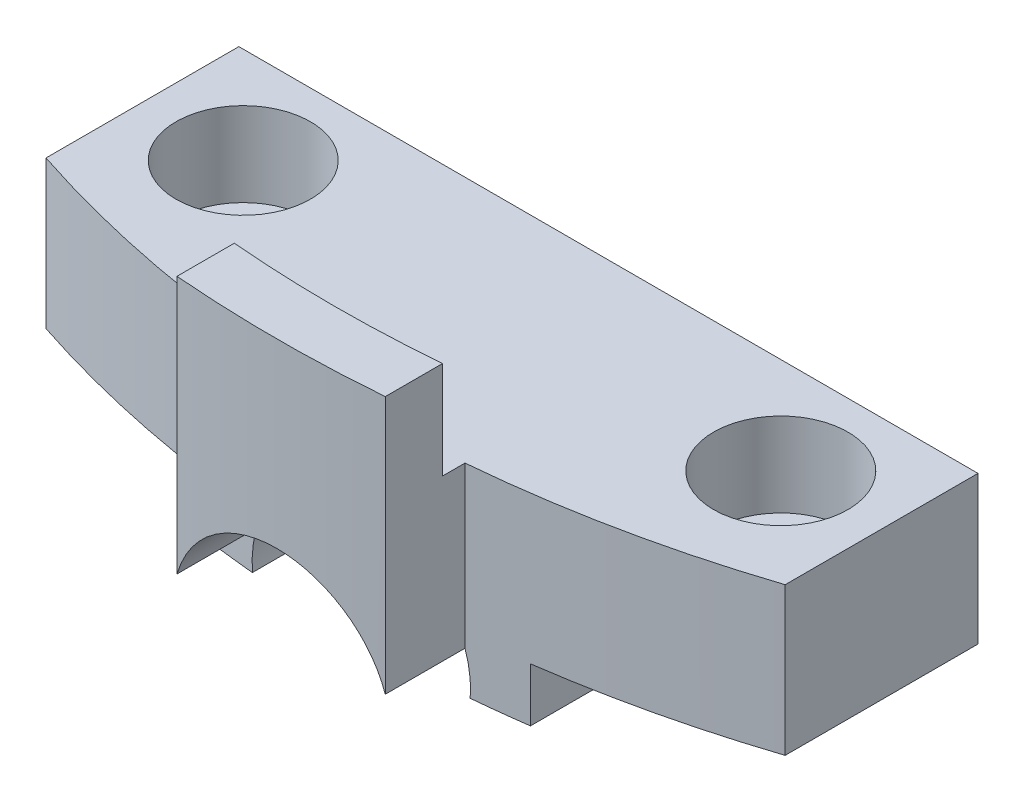
SolidWorks part; units mm, degrees
ref_plane "Front Plane" through (0, 0, 0) normal (0, 0, 1) x (1, 0, 0)
ref_plane "Top Plane" through (0, 0, 0) normal (0, 1, 0) x (1, 0, 0)
ref_plane "Right Plane" through (0, 0, 0) normal (1, 0, 0) x (0, 0, -1)
sketch "Sketch1" plane through (0, 0, 0) normal (0, 1, 0) x (1, 0, 0)
  line L0 (-8, -30.5) -> (8, -30.5) construction
  line L1 (-3.1, -37.3716) -> (-3.1, -34.999)
  line L2 (-11, -27.6303) -> (11, -27.6303)
  line L3 (-11, -27.6303) -> (-11, -33.3697)
  line L5 (11, -27.6303) -> (11, -33.3697)
  line L6 (3.1, -37.3716) -> (3.1, -34.999)
  circle A0 centre (-8, -30.5) radius 1.1
  circle A1 centre (8, -30.5) radius 1.1
  arc A2 (11, -33.3697) -> (3.1, -34.999) centre (0, 0) cw
  arc A3 (-3.1, -37.3716) -> (3.1, -37.3716) centre (0, 0) ccw
  arc A4 (-3.1, -34.999) -> (-11, -33.3697) centre (0, 0) cw
  point P4 (0, -30.5)
  point P10 (0, -27.6303)
  point P12 (-11, -30.5)
  point P15 (0, -37.5)
  dimension "D2" = 2.2
  dimension "D5" = 35.136
  dimension "D6" = 37.5
  dimension "D1" = 16
  dimension "D3" = 22
  dimension "D4" = 30.5
  dimension "D7" = 6.2
extrude "Boss-Extrude1" add sketch "Sketch1" along normal blind 4.4
sketch "Sketch2" plane through (0, 4.4, 0) normal (0, 1, 0) x (1, 0, 0)
  line L0 (-3.1, -34.999) -> (-3.1, -37.3716) construction
  line L1 (3.1, -37.3716) -> (3.1, -34.999) construction
  line L2 (3.1, -37.3716) -> (3.1, -35.6655)
  line L3 (-3.1, -35.6655) -> (-3.1, -37.3716)
  arc A0 (-3.1, -35.6655) -> (3.1, -35.6655) centre (0, 0) ccw
  arc A1 (-3.1, -37.3716) -> (3.1, -37.3716) centre (0, 0) ccw construction
  arc A2 (-3.1, -37.3716) -> (3.1, -37.3716) centre (0, 0) ccw
  dimension "D1" = 35.8
extrude "Boss-Extrude2" add sketch "Sketch2" along normal blind 2.9
sketch "Sketch3" plane through (0, 4.4, 0) normal (0, 1, 0) x (1, 0, 0)
  circle A0 centre (-8, -30.5) radius 2
  circle A1 centre (8, -30.5) radius 2
  dimension "D1" = 4
extrude "Cut-Extrude1" cut sketch "Sketch3" against normal blind 2.5
sketch "Sketch5" plane through (0, 0, 0) normal (0, -1, 0) x (1, 0, 0)
  line L0 (-4.85, 34.7997) -> (-4.85, 27.6303)
  line L1 (11, 27.6303) -> (-11, 27.6303) construction
  line L2 (4.85, 34.7997) -> (4.85, 27.6303)
  line L5 (-11, 33.3697) -> (-11, 27.6303)
  line L6 (-11, 27.6303) -> (11, 27.6303)
  line L7 (11, 27.6303) -> (11, 33.3697)
  line L8 (3.1, 34.999) -> (3.1, 37.3716)
  line L9 (-3.1, 37.3716) -> (-3.1, 34.999)
  line L11 (-4.85, 27.6303) -> (4.85, 27.6303)
  line L13 (3.1, 34.999) -> (3.1, 37.3716)
  line L14 (-3.1, 37.3716) -> (-3.1, 34.999)
  arc A3 (11, 33.3697) -> (3.1, 34.999) centre (0, 0) ccw
  arc A4 (3.1, 37.3716) -> (-3.1, 37.3716) centre (0, 0) ccw
  arc A5 (-3.1, 34.999) -> (-11, 33.3697) centre (0, 0) ccw
  arc A6 (4.85, 34.7997) -> (3.1, 34.999) centre (0, 0) ccw
  arc A7 (3.1, 37.3716) -> (-3.1, 37.3716) centre (0, 0) ccw
  arc A8 (-3.1, 34.999) -> (-4.85, 34.7997) centre (0, 0) ccw
  point P11 (0, 27.6303)
  dimension "D2" = 9.7
  dimension "D1" = 0
extrude "Boss-Extrude3" add sketch "Sketch5" along normal blind 1.6
sketch "Sketch6" plane through (0, 0, 27.6303) normal (0, 0, -1) x (-1, 0, 0)
  line L0 (0, -1.6) -> (0, -4.6) construction
  line L1 (4.85, -1.6) -> (-4.85, -1.6) construction
  circle A0 centre (0, -1.35) radius 3.25
  dimension "D1" = 6.5
  dimension "D2" = 3
extrude "Cut-Extrude2" cut sketch "Sketch6" against normal through all
